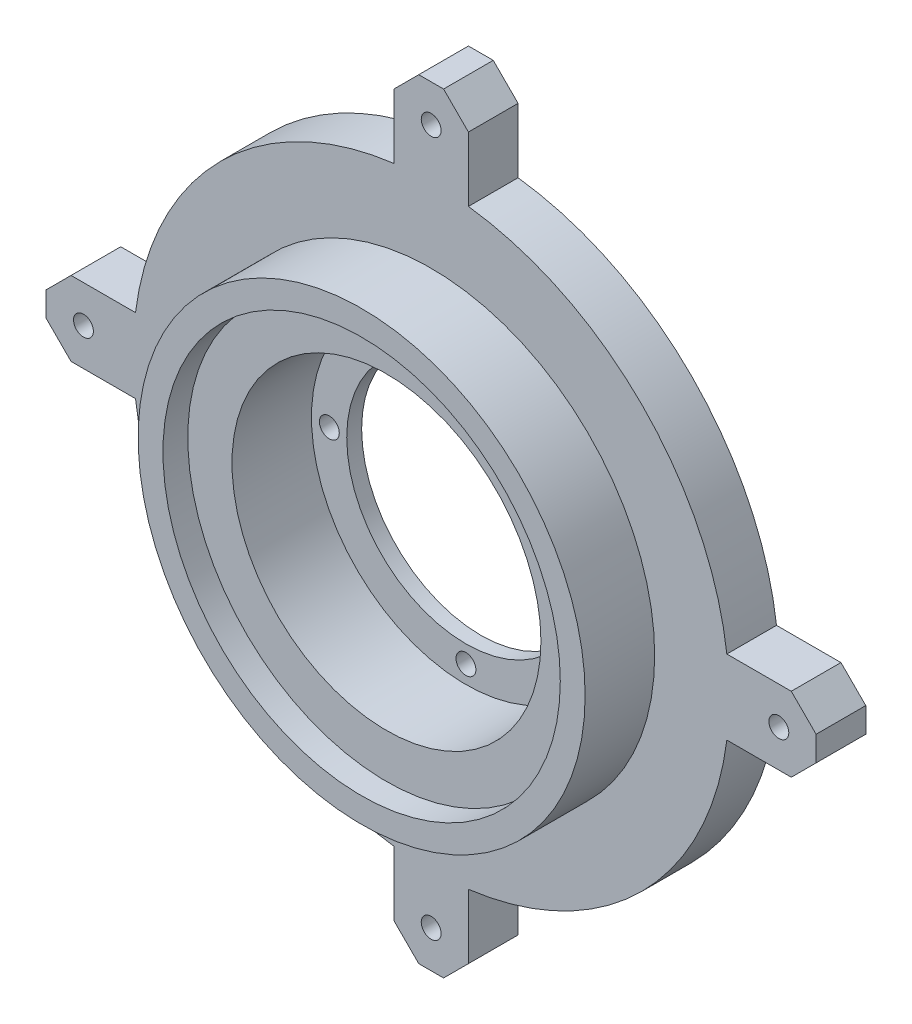
SolidWorks part; units mm, degrees
ref_plane "Front Plane" through (0, 0, 0) normal (0, 0, 1) x (1, 0, 0)
ref_plane "Top Plane" through (0, 0, 0) normal (0, 1, 0) x (1, 0, 0)
ref_plane "Right Plane" through (0, 0, 0) normal (1, 0, 0) x (0, 0, -1)
sketch "Sketch1" plane through (0, 0, 0) normal (0, 0, 1) x (1, 0, 0)
  line L0 (-72.5, 7.5) -> (-77.5, 2.5)
  line L1 (-42.5, -7.5) -> (-72.5, -7.5)
  line L2 (-42.5, -7.5) -> (-42.5, 7.5)
  line L3 (-42.5, 7.5) -> (-72.5, 7.5)
  line L4 (-77.5, -2.5) -> (-77.5, 2.5)
  line L5 (-42.5, -7.5) -> (-77.5, 7.5) construction
  line L6 (-42.5, 7.5) -> (-77.5, -7.5) construction
  line L7 (-72.5, -7.5) -> (-77.5, -2.5)
  line L8 (-7.5, 42.5) -> (7.5, 42.5)
  line L9 (-7.5, 42.5) -> (-7.5, 72.5)
  line L10 (-7.5, 72.5) -> (-2.5, 77.5)
  line L11 (-2.5, 77.5) -> (2.5, 77.5)
  line L12 (7.5, 72.5) -> (2.5, 77.5)
  line L13 (7.5, 42.5) -> (7.5, 72.5)
  line L14 (42.5, 7.5) -> (42.5, -7.5)
  line L15 (42.5, 7.5) -> (72.5, 7.5)
  line L16 (72.5, 7.5) -> (77.5, 2.5)
  line L17 (77.5, 2.5) -> (77.5, -2.5)
  line L18 (72.5, -7.5) -> (77.5, -2.5)
  line L19 (42.5, -7.5) -> (72.5, -7.5)
  line L20 (7.5, -42.5) -> (-7.5, -42.5)
  line L21 (7.5, -42.5) -> (7.5, -72.5)
  line L22 (7.5, -72.5) -> (2.5, -77.5)
  line L23 (2.5, -77.5) -> (-2.5, -77.5)
  line L24 (-7.5, -72.5) -> (-2.5, -77.5)
  line L25 (-7.5, -42.5) -> (-7.5, -72.5)
  circle A0 centre (0, 0) radius 60
  point P3 (-60, 0)
  point P33 (0, 0)
  dimension "D1" = 120
  dimension "D2" = 35
  dimension "D3" = 15
  dimension "D4" = 4
extrude "Boss-Extrude1" add sketch "Sketch1" along normal blind 10 contours L3 A0 L1 L2 | L15 A0 L13 L8 L9 L3 L2 L1 L25 L20 L21 L19 L14 | L13 A0 L9 L8 | A0 L13 L12 L11 L10 L9 | A0 L3 L0 L4 L7 L1 | L19 A0 L15 L14 | A0 L19 L18 L17 L16 L15 | A0 L25 L24 L23 L22 L21 | L25 A0 L21 L20
sketch "Sketch2" plane through (0, 0, 10) normal (0, 0, 1) x (1, 0, 0)
  circle A0 centre (0, 0) radius 45
  dimension "D1" = 90
extrude "Boss-Extrude2" add sketch "Sketch2" along normal blind 14
sketch "Sketch3" plane through (0, 0, 24) normal (0, 0, 1) x (1, 0, 0)
  circle A0 centre (0, 0) radius 31.1
  dimension "D1" = 62.2
extrude "Cut-Extrude1" cut sketch "Sketch3" against normal blind 21
sketch "Sketch4" plane through (0, 0, 0) normal (0, 0, -1) x (-1, 0, 0)
  circle A2 centre (0, 0) radius 24
  dimension "D1" = 48
hole_wizard "Ø4.0mm Dowel Hole1" positions "Sketch10" profile "Sketch6" hole size "Ø4.0" standard "ANSI Metric" end condition through all
sketch "Sketch10" plane through (0, 0, 0) normal (0, 0, -1) x (-1, 0, 0)
  point P4 (-70, 0)
  point P10 (0, 70)
  point P11 (70, 0)
  point P12 (0, -70)
  dimension "D2" = 70
  dimension "D1" = 4
sketch "Sketch6" plane through (70, 0, 0) normal (1, 0, 0) x (0, 1, 0)
  line L0 (0, 0) -> (0, 24)
  line L1 (0, 24) -> (2, 24)
  line L2 (2, 24) -> (2, 0.025)
  line L3 (2, 0.025) -> (2.025, 0)
  line L5 (2.025, 0) -> (0, 0)
  line L6 (-2, 0.025) -> (-2.025, 0) construction
  line L11 (0, -6.35) -> (0, 107.95) construction
  dimension "Thru Hole Dia." = 4
  dimension "Thru Hole Depth" = 24
  dimension "Near C'Sink Dia." = 4.05
  dimension "Near C'Sink Angle" = 90
sketch "Sketch11" plane through (0, 0, 24) normal (0, 0, 1) x (1, 0, 0)
  circle A0 centre (0, 0) radius 40
extrude "Cut-Extrude2" cut sketch "Sketch11" against normal blind 5
extrude "Cut-Extrude3" cut sketch "Sketch4" against normal blind 4
sketch "Sketch12" plane through (0, 0, 0) normal (0, 0, -1) x (-1, 0, 0)
  circle A0 centre (27.5, 0) radius 2
  circle A1 centre (0, -27.5) radius 2
  circle A2 centre (-27.5, 0) radius 2
  circle A3 centre (0, 27.5) radius 2
  point P12 (0, 0)
  dimension "D1" = 27.5
  dimension "D2" = 4
extrude "Cut-Extrude5" cut sketch "Sketch12" against normal blind 4
